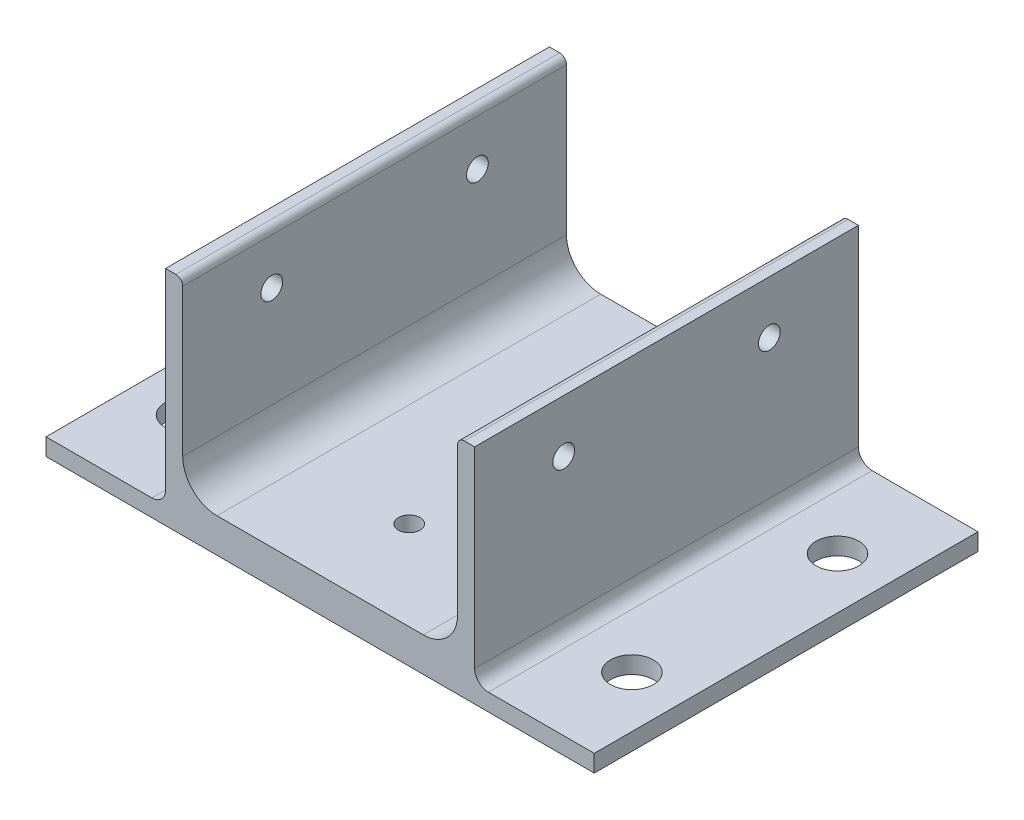
SolidWorks part; units mm, degrees
ref_plane "Front" through (0, 0, 0) normal (0, 0, 1) x (1, 0, 0)
ref_plane "Top" through (0, 0, 0) normal (0, 1, 0) x (1, 0, 0)
ref_plane "Right" through (0, 0, 0) normal (1, 0, 0) x (0, 0, -1)
sketch "Sketch1" plane through (0, 0, 0) normal (0, 0, 1) x (1, 0, 0)
  line L0 (0, 0) -> (0, 34.925)
  line L1 (0, 34.925) -> (-3.175, 34.925)
  line L2 (-3.175, 34.925) -> (-3.175, -3.175)
  line L3 (-3.175, -3.175) -> (34.925, -3.175)
  line L4 (34.925, -3.175) -> (34.925, 0)
  line L5 (34.925, 0) -> (0, 0)
  dimension "Height" = 38.1
  dimension "Width" = 38.1
  dimension "Wall Thickness" = 3.175
sketch "Sketch3" plane through (0, 0, 0) normal (0, 0, 1) x (1, 0, 0)
  line L0 (0, 0) -> (0, 34.925) construction
  line L1 (0, 34.925) -> (-3.175, 34.925) construction
  line L2 (-3.175, 34.925) -> (-3.175, -3.175) construction
  line L3 (-3.175, -3.175) -> (34.925, -3.175) construction
  line L4 (34.925, -3.175) -> (34.925, 0) construction
  line L5 (34.925, 0) -> (0, 0) construction
  line L6 (0, 6.35) -> (0, 33.655)
  line L7 (-1.27, 34.925) -> (-3.175, 34.925)
  line L8 (-3.175, 34.925) -> (-3.175, 0)
  line L9 (-3.175, -3.175) -> (34.925, -3.175)
  line L10 (34.925, -3.175) -> (34.925, -1.27)
  line L11 (33.655, 0) -> (6.35, 0)
  line L12 (-3.175, -3.175) -> (-3.175, 0)
  arc A0 (0, 6.35) -> (6.35, 0) centre (6.35, 6.35) ccw
  arc A1 (34.925, -1.27) -> (33.655, 0) centre (33.655, -1.27) ccw
  arc A2 (0, 33.655) -> (-1.27, 34.925) centre (-1.27, 33.655) ccw
  dimension "D1" = 1.27
  dimension "D2" = 6.35
extrude "Boss-Extrude1" add sketch "Sketch3" along normal blind 71.12
sketch "Sketch4" plane through (0, 0, 0) normal (0, 0, -1) x (-1, 0, 0)
  line L0 (3.175, -3.175) -> (-34.925, -3.175) construction
  line L1 (-25.4635, -3.175) -> (-34.925, -3.175)
  line L2 (-25.4635, -3.175) -> (-25.4635, 0)
  line L3 (-25.4635, 0) -> (-34.925, 0)
  line L4 (-34.925, -3.175) -> (-34.925, 0)
  line L5 (0, 6.35) -> (0, 33.655) construction
  line L6 (-34.925, -3.175) -> (-34.925, -1.27) construction
  dimension "D1" = 3.175
  dimension "D2" = 25.4635
extrude "Cut-Extrude1" cut sketch "Sketch4" against normal through all
sketch "Sketch5" plane through (0, 0, 0) normal (0, 0, -1) x (-1, 0, 0)
  line L0 (-25.4635, -3.175) -> (-54.102, -3.175)
  line L1 (-54.102, -3.175) -> (-54.102, 34.925)
  line L2 (-54.102, 34.925) -> (-50.927, 34.925)
  line L3 (-50.927, 34.925) -> (-50.927, 0)
  line L4 (-50.927, 0) -> (-25.4635, 0)
  line L5 (-25.4635, 0) -> (-25.4635, -3.175)
  line L6 (1.27, 34.925) -> (3.175, 34.925) construction
  dimension "D1" = 25.4635
  dimension "D2" = 3.175
extrude "Boss-Extrude2" add sketch "Sketch5" against normal blind 71.12
fillet "Fillet2" radius 6.35 1 edges at (50.927, 0, 35.56)
fillet "Fillet4" radius 1.27 1 edges at (50.927, 34.925, 35.56)
sketch "Sketch6" plane through (0, -3.175, 0) normal (0, -1, 0) x (1, 0, 0)
  line L1 (-25.3365, 71.12) -> (76.2635, 71.12)
  line L2 (-25.3365, 71.12) -> (-25.3365, 0)
  line L3 (-25.3365, 0) -> (76.2635, 0)
  line L4 (76.2635, 71.12) -> (76.2635, 0)
  line L7 (54.102, 71.12) -> (54.102, 0) construction
  line L8 (44.577, 71.12) -> (6.35, 71.12) construction
  dimension "D1" = 101.6
  dimension "D2" = 71.12
  dimension "D3" = 22.1615
extrude "Boss-Extrude3" add sketch "Sketch6" along normal blind 3.175
sketch "Sketch7" plane through (-3.175, 0, 0) normal (-1, 0, 0) x (0, 0, 1)
  line L0 (71.12, 34.925) -> (0, 34.925) construction
  line L3 (0, 34.925) -> (0, -3.175) construction
  circle A0 centre (16.51, 25.146) radius 2.0193
  circle A1 centre (54.61, 25.146) radius 2.0193
  dimension "D1" = 9.779
  dimension "D4" = 4.0386
  dimension "D2" = 38.1
  dimension "D3" = 16.51
extrude "Cut-Extrude2" cut sketch "Sketch7" against normal through all
sketch "Sketch8" plane through (0, -6.35, 0) normal (0, -1, 0) x (1, 0, 0)
  line L1 (-25.3365, 0) -> (76.2635, 0) construction
  line L2 (76.2635, 0) -> (76.2635, 71.12) construction
  circle A0 centre (25.4635, 16.51) radius 2.0193
  circle A1 centre (25.4635, 54.61) radius 2.0193
  dimension "D1" = 38.1
  dimension "D3" = 4.0386
  dimension "D2" = 16.51
  dimension "D4" = 50.8
extrude "Cut-Extrude3" cut sketch "Sketch8" against normal through all
sketch "Sketch9" plane through (0, -6.35, 0) normal (0, -1, 0) x (1, 0, 0)
  line L0 (76.2635, 71.12) -> (-25.3365, 71.12) construction
  line L1 (76.2635, 0) -> (76.2635, 71.12) construction
  circle A0 centre (-15.8115, 16.51) radius 3.9688
  circle A1 centre (-15.8115, 54.61) radius 3.9688
  circle A2 centre (66.7385, 54.61) radius 3.9687
  circle A3 centre (66.7385, 16.51) radius 3.9687
  dimension "D1" = 7.9375
  dimension "D2" = 38.1
  dimension "D3" = 16.51
  dimension "D4" = 82.55
  dimension "D5" = 9.525
extrude "Cut-Extrude4" cut sketch "Sketch9" against normal through all
fillet "Fillet5" radius 2.54 2 edges at (-3.175, -3.175, 35.56) (54.102, -3.175, 35.56)
sketch "Sketch10" plane through (0, -6.35, 0) normal (0, -1, 0) x (1, 0, 0)
  circle A0 centre (25.4635, 54.61) radius 5.08
  circle A1 centre (25.4635, 16.51) radius 5.08
  dimension "D1" = 10.16
  dimension "D2" = 10.16
extrude "Cut-Extrude5" cut sketch "Sketch10" against normal blind 3.175
equation "\"D1@Sketch3\"=\"Wall Thickness@Sketch1\"*0.4"
equation "\"D2@Sketch3\"=\"Wall Thickness@Sketch1\"*2"
